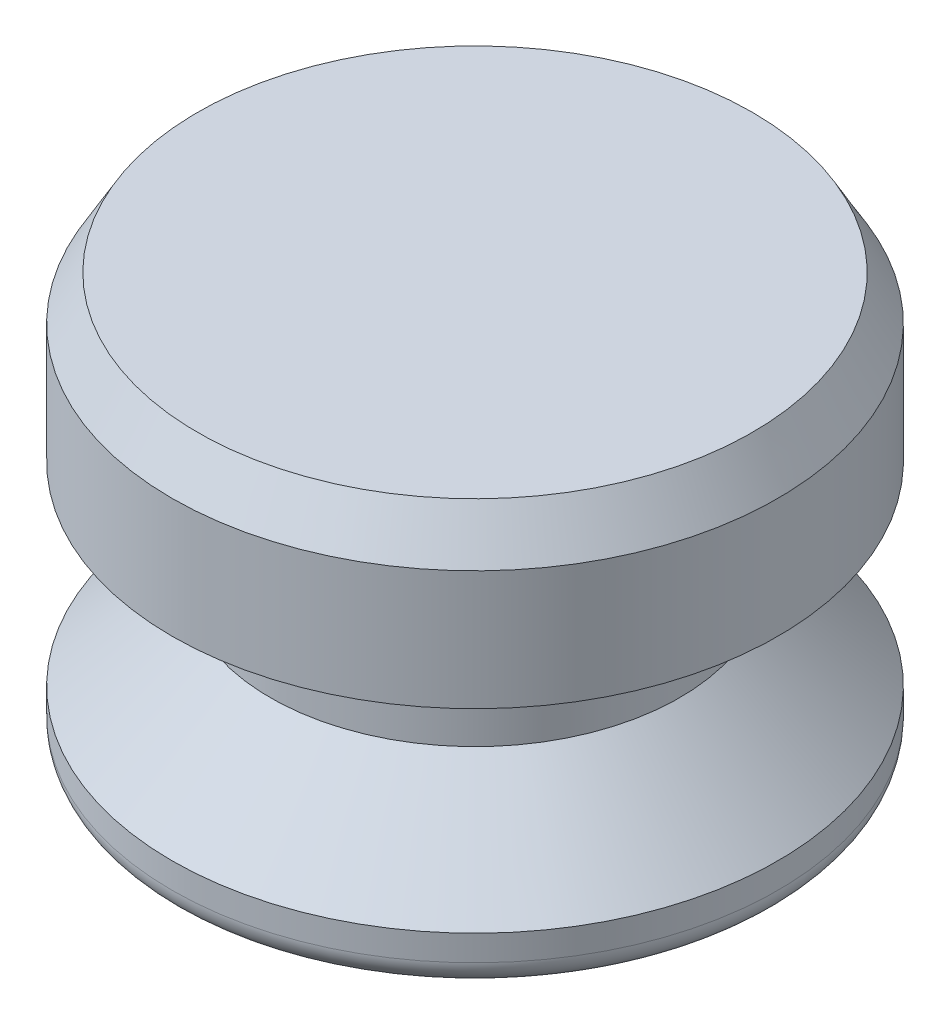
SolidWorks part; units mm, degrees
ref_plane "Front Plane" through (0, 0, 0) normal (0, 0, 1) x (1, 0, 0)
ref_plane "Top Plane" through (0, 0, 0) normal (0, 1, 0) x (1, 0, 0)
ref_plane "Right Plane" through (0, 0, 0) normal (1, 0, 0) x (0, 0, -1)
sketch "Sketch1" plane through (0, 0, 0) normal (0, 0, 1) x (1, 0, 0)
  line L0 (0, 0) -> (0, 12.7) construction
  line L1 (0, 0) -> (-9.398, 0)
  line L2 (-9.398, 0) -> (-9.398, 1.5875)
  line L4 (-6.35, 4.445) -> (-6.35, 7.62)
  line L5 (-6.35, 7.62) -> (-9.398, 7.62)
  line L6 (-9.398, 7.62) -> (-9.398, 12.7)
  line L7 (-9.398, 12.7) -> (0, 12.7)
  line L8 (-9.525, 16.6801) -> (-9.525, -9.6051) construction
  line L9 (0, 0) -> (0, 12.7)
  line L10 (-6.35, 4.445) -> (-9.398, 1.5875)
  dimension "D1" = 12.7
  dimension "D2" = 9.398
  dimension "D3" = 3.175
  dimension "D4" = 1.5875
  dimension "D5" = 9.525
  dimension "D6" = 6.35
  dimension "D7" = 7.62
revolve "Revolve1" add sketch "Sketch1" angle 360 about L9
fillet "Fillet1" radius 0.7937 1 edges at (0, 0, -9.398)
chamfer "Chamfer1" distance 0.7937 angle 60 1 edges at (0, 12.7, -9.398)
